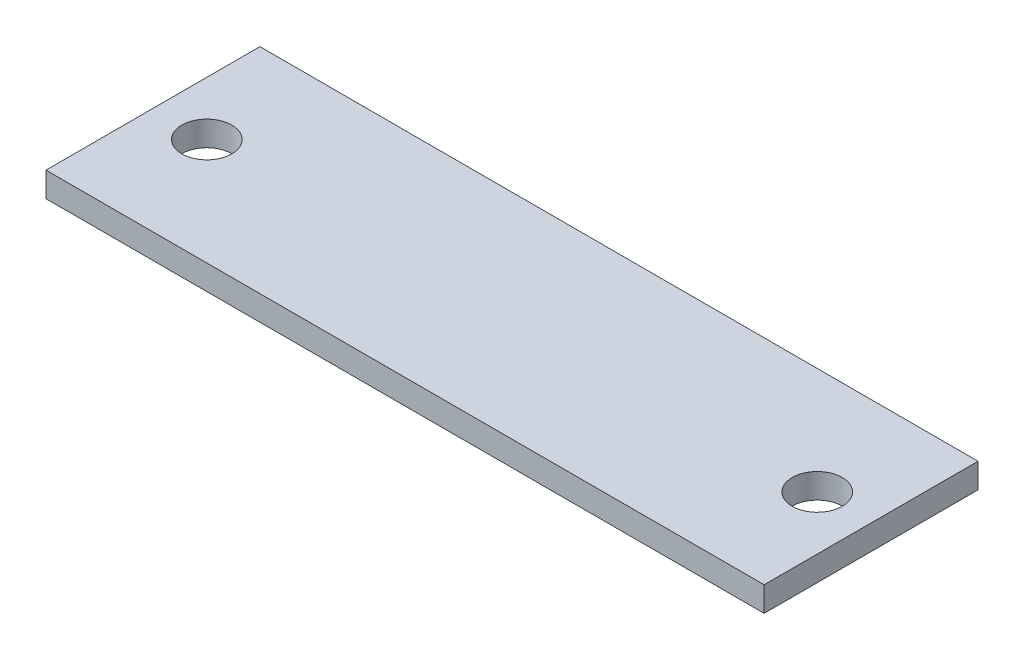
SolidWorks part; units mm, degrees
ref_plane "Front Plane" through (0, 0, 0) normal (0, 0, 1) x (1, 0, 0)
ref_plane "Top Plane" through (0, 0, 0) normal (0, 1, 0) x (1, 0, 0)
ref_plane "Right Plane" through (0, 0, 0) normal (1, 0, 0) x (0, 0, -1)
sketch "Sketch1" plane through (0, 0, 0) normal (0, 1, 0) x (1, 0, 0)
  line L0 (-19.55, 0) -> (0, 0) construction
  line L1 (-23, -6.85) -> (23, -6.85)
  line L2 (-23, -6.85) -> (-23, 6.85)
  line L3 (-23, 6.85) -> (23, 6.85)
  line L4 (23, -6.85) -> (23, 6.85)
  line L5 (-23, -6.85) -> (23, 6.85) construction
  line L6 (-23, 6.85) -> (23, -6.85) construction
  line L7 (0, 0) -> (19.55, 0) construction
  circle A0 centre (-19.55, 0) radius 1.6
  circle A1 centre (19.55, 0) radius 1.6
  point P0 (0, 0)
  dimension "D4" = 3.2
  dimension "D1" = 13.7
  dimension "D2" = 46
  dimension "D3" = 39.1
extrude "Boss-Extrude1" add sketch "Sketch1" along normal mid plane 1.5875
equation "\"D1@Sketch1\"=13.7mm"
equation "\"D3@Sketch1\"=39.1mm"
equation "\"D2@Sketch1\"=46mm"
equation "\"D4@Sketch1\"=3.2mm"
